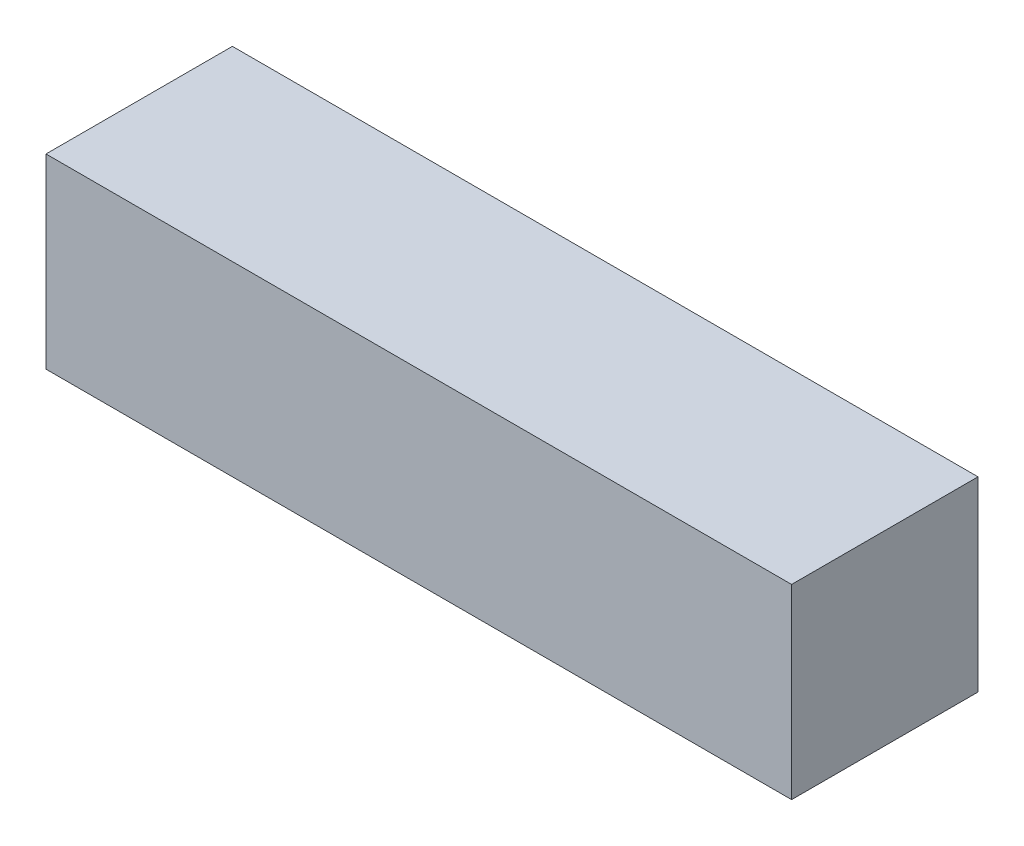
SolidWorks part; units mm, degrees
ref_plane "Alzado" through (0, 0, 0) normal (0, 0, 1) x (1, 0, 0)
ref_plane "Planta" through (0, 0, 0) normal (0, 1, 0) x (1, 0, 0)
ref_plane "Vista lateral" through (0, 0, 0) normal (1, 0, 0) x (0, 0, -1)
sketch "Croquis1" plane through (0, 0, 0) normal (0, 1, 0) x (1, 0, 0)
  line L1 (-12, 3) -> (12, 3)
  line L2 (-12, 3) -> (-12, -3)
  line L3 (-12, -3) -> (12, -3)
  line L4 (12, 3) -> (12, -3)
  line L5 (-12, 3) -> (12, -3) construction
  line L6 (-12, -3) -> (12, 3) construction
  point P0 (0, 0)
  dimension "D1" = 24
  dimension "D2" = 6
extrude "Saliente-Extruir1" add sketch "Croquis1" along normal blind 6
